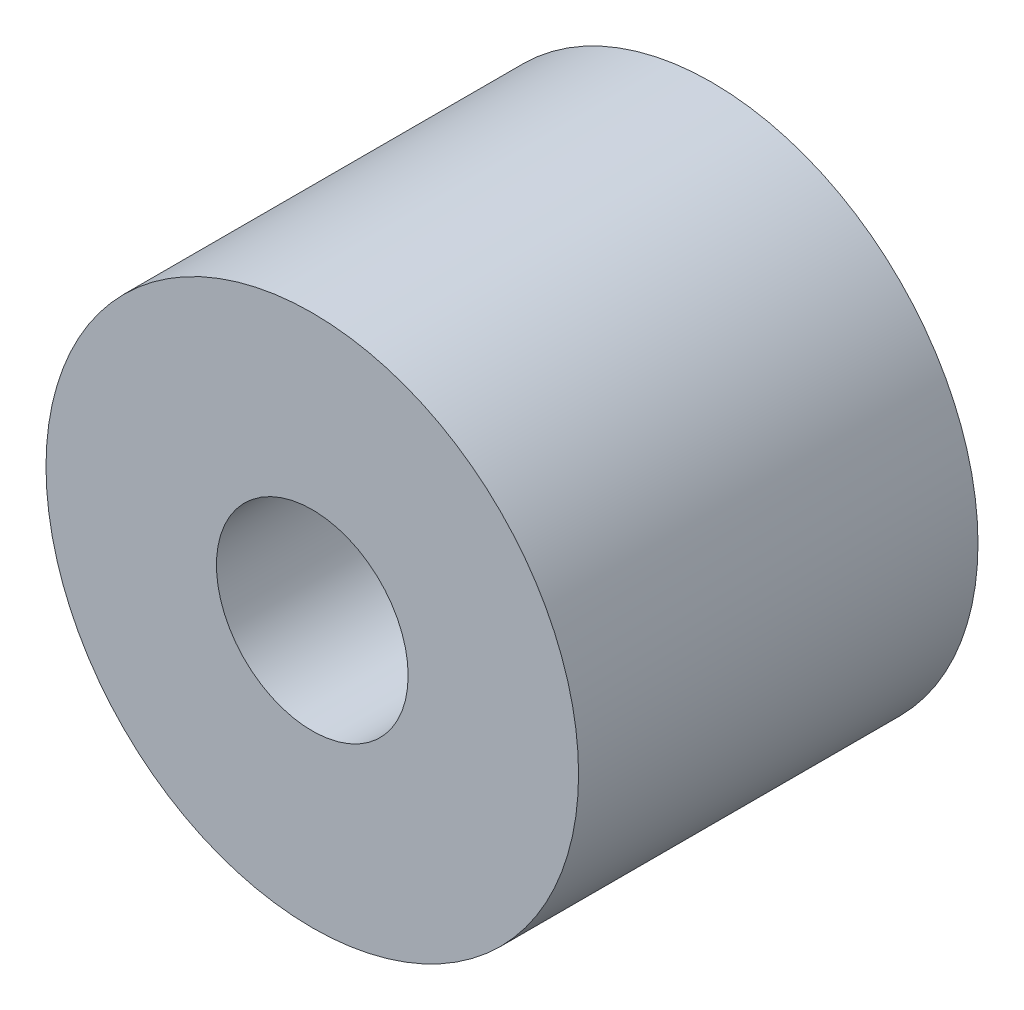
SolidWorks part; units mm, degrees
ref_plane "Front Plane" through (0, 0, 0) normal (0, 0, 1) x (1, 0, 0)
ref_plane "Top Plane" through (0, 0, 0) normal (0, 1, 0) x (1, 0, 0)
ref_plane "Right Plane" through (0, 0, 0) normal (1, 0, 0) x (0, 0, -1)
sketch "Sketch1" plane through (0, 0, 0) normal (0, 0, 1) x (1, 0, 0)
  line L0 (0, 1.143) -> (0, 3.175) construction
  line L1 (0, -1.143) -> (0, -3.175) construction
  circle A0 centre (0, 0) radius 3.175
  circle A1 centre (0, 0) radius 1.143
  dimension "OD" = 6.35
  dimension "ID" = 2.286
sketch "Sketch2" plane through (0, 0, 0) normal (1, 0, 0) x (0, 0, -1)
  line L0 (-2.3813, 1.143) -> (2.3813, 1.143) construction
  line L1 (-2.3813, -1.143) -> (2.3813, -1.143) construction
  line L2 (-2.3813, -3.175) -> (2.3813, -3.175) construction
  line L3 (-2.3813, 3.175) -> (2.3813, 3.175) construction
  dimension "Length" = 4.7625
extrude "Extrude1" add sketch "Sketch1" along normal up to vertex (2.3813 mm away) and the other way up to vertex (2.3813 mm away) up to point (0, 1.143, 2.3813) other way up to point (0, 1.143, -2.3813)
sketch "Sketch3" plane through (0, 0, 2.3813) normal (0, 0, 1) x (1, 0, 0)
  circle A0 centre (0, 0) radius 1.143 construction
  circle A3 centre (0, 0) radius 1.143
  point P3 (-1.143, 0)
